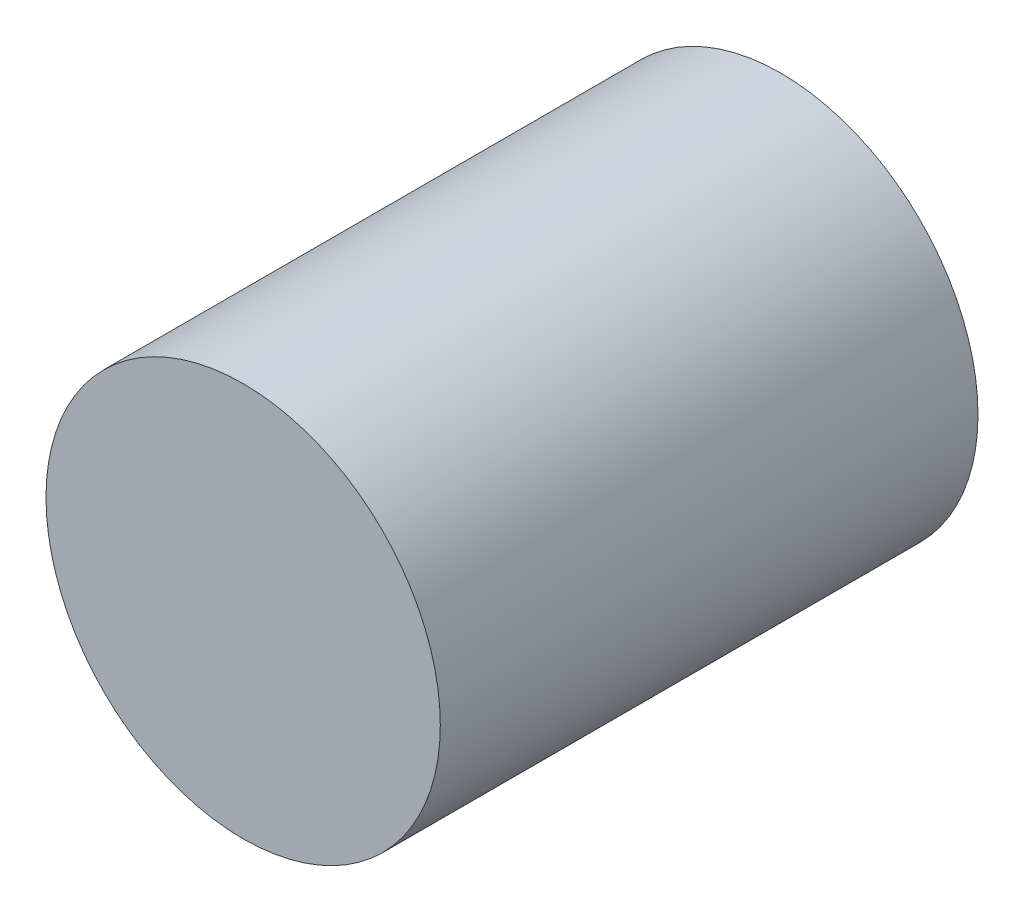
SolidWorks part; units mm, degrees
ref_plane "Front Plane" through (0, 0, 0) normal (0, 0, 1) x (1, 0, 0)
ref_plane "Top Plane" through (0, 0, 0) normal (0, 1, 0) x (1, 0, 0)
ref_plane "Right Plane" through (0, 0, 0) normal (1, 0, 0) x (0, 0, -1)
sketch "Sketch1" plane through (0, 0, 0) normal (0, 0, 1) x (1, 0, 0)
  circle A0 centre (0, -206.1) radius 27.5 construction
  circle A1 centre (0, -206.1) radius 27.5
extrude "Boss-Extrude1" add sketch "Sketch1" along normal up to surface (44 mm away) and the other way up to surface (31 mm away)
sketch "Sketch2" plane through (0, 0, -31) normal (0, 0, -1) x (-1, 0, 0)
  line L0 (27.5, -206.1) -> (-27.5, -206.1) construction
  line L1 (22.5, -206.1) -> (5.5, -191.1)
  line L2 (5.5, -191.1) -> (5.5, -201.1)
  line L3 (5.5, -201.1) -> (-19.5, -201.1)
  line L4 (-19.5, -201.1) -> (-19.5, -211.1)
  line L5 (-19.5, -211.1) -> (5.5, -211.1)
  line L6 (5.5, -211.1) -> (5.5, -221.1)
  line L7 (5.5, -221.1) -> (22.5, -206.1)
  line L8 (5.5, -201.1) -> (5.5, -206.1) construction
  line L9 (5.5, -206.1) -> (5.5, -211.1) construction
  circle A0 centre (0, -206.1) radius 27.5 construction
  dimension "D1" = 10
  dimension "D2" = 30
  dimension "D3" = 8
  dimension "D4" = 5
  dimension "D5" = 25
extrude "Cut-Extrude1" cut sketch "Sketch2" against normal blind 10
